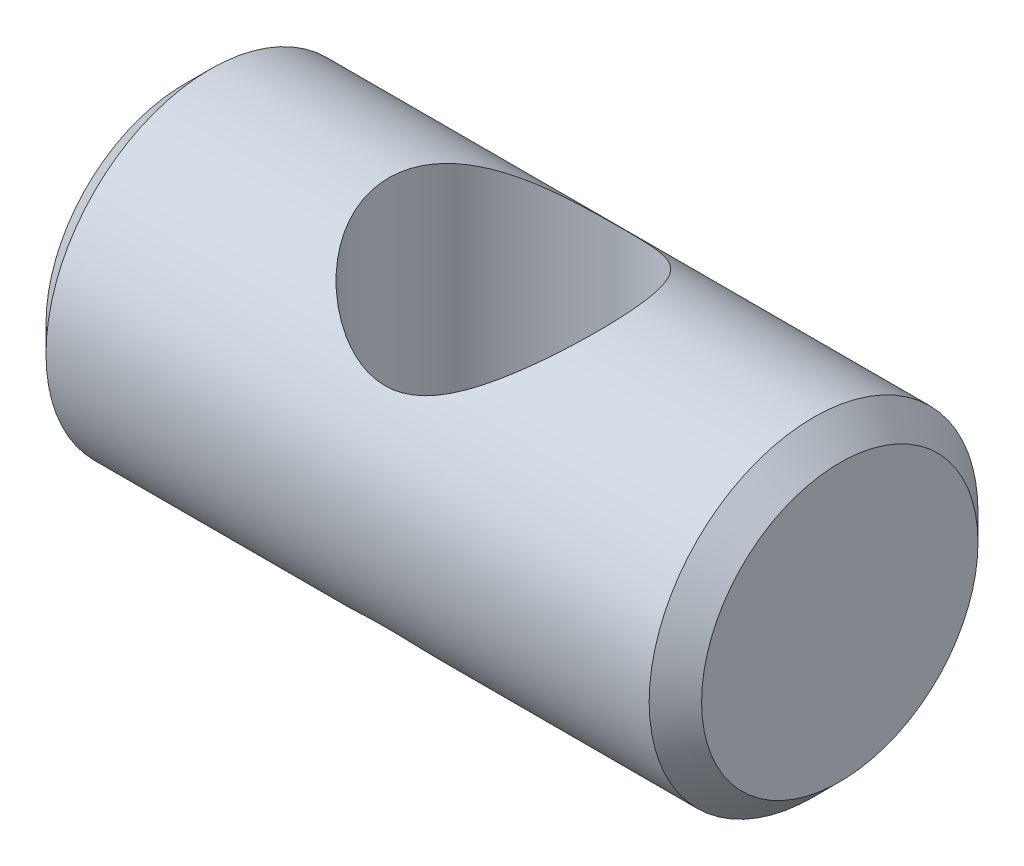
SolidWorks part; units mm, degrees
material "1023 Carbon Steel Sheet (SS)"
ref_plane "Front Plane" through (0, 0, 0) normal (0, 0, 1) x (1, 0, 0)
ref_plane "Top Plane" through (0, 0, 0) normal (0, 1, 0) x (1, 0, 0)
ref_plane "Right Plane" through (0, 0, 0) normal (1, 0, 0) x (0, 0, -1)
sketch "Sketch1" plane through (0, 0, 0) normal (1, 0, 0) x (0, 0, -1)
  circle A0 centre (0, 0) radius 4.765
  dimension "D1" = 9.53
extrude "Boss-Extrude1" add sketch "Sketch1" along normal mid plane 19
chamfer "Chamfer1" distance 0.76 angle 45 2 edges at (-9.5, 0, -4.765) (9.5, 0, -4.765)
sketch "Sketch2" plane through (0, 0, 0) normal (0, 1, 0) x (1, 0, 0)
  circle A0 centre (0, -0.25) radius 3.43
  dimension "D1" = 6.86
  dimension "D2" = 0.25
extrude "Cut-Extrude1" cut sketch "Sketch2" against normal through all both and the other way through all
